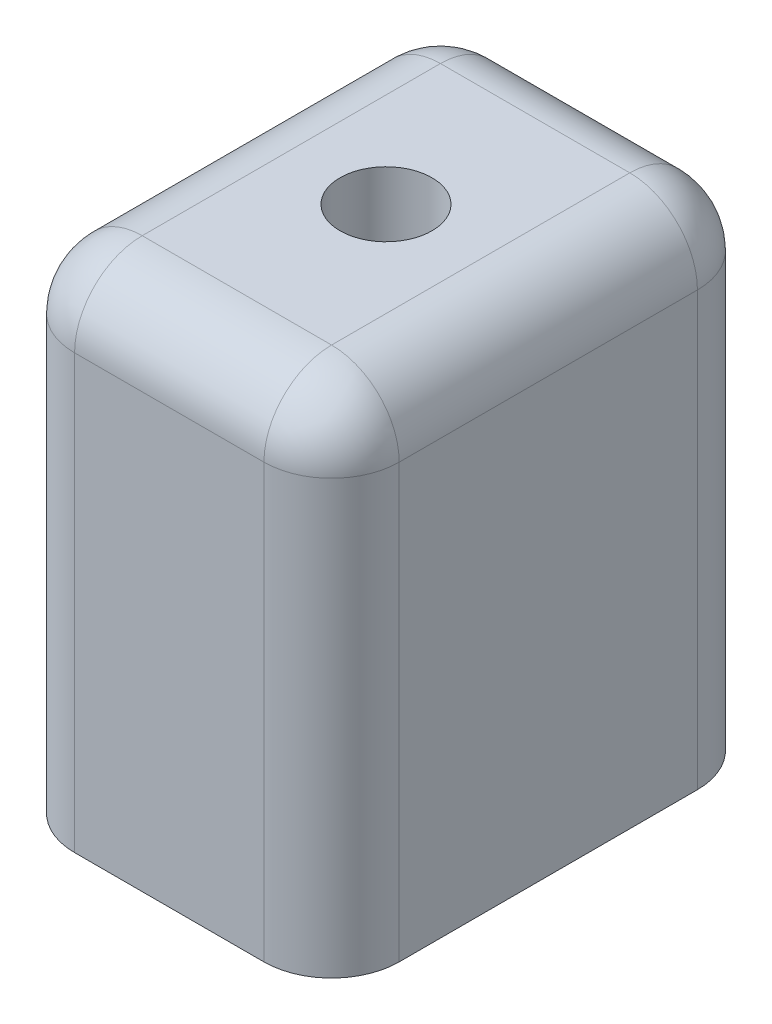
SolidWorks part; units mm, degrees
ref_plane "Front Plane" through (0, 0, 0) normal (0, 0, 1) x (1, 0, 0)
ref_plane "Top Plane" through (0, 0, 0) normal (0, 1, 0) x (1, 0, 0)
ref_plane "Right Plane" through (0, 0, 0) normal (1, 0, 0) x (0, 0, -1)
sketch "Sketch1" plane through (0, 0, 0) normal (0, 1, 0) x (1, 0, 0)
  line L5 (-1.9438, 25.0455) -> (22.0562, 25.0455)
  line L6 (-1.9438, 25.0455) -> (-1.9438, -7.0045)
  line L7 (-1.9438, -7.0045) -> (22.0562, -7.0045)
  line L8 (22.0562, 25.0455) -> (22.0562, -7.0045)
  circle A0 centre (5.0562, 9.0205) radius 2.15
  circle A1 centre (15.0562, 9.0205) radius 2.15
  circle A2 centre (10.0562, 19.8955) radius 2.15
  circle A3 centre (10.0562, -1.8545) radius 2.15
  point P13 (22.0562, 9.0205)
  dimension "D1" = 4.3
  dimension "D2" = 4.3
  dimension "D6" = 4.3
  dimension "D7" = 4.3
  dimension "D10" = 7
  dimension "D3" = 10
  dimension "D4" = 5
  dimension "D5" = 5
  dimension "D8" = 21.75
  dimension "D9" = 10.875
  dimension "D11" = 7
  dimension "D12" = 24
  dimension "D13" = 5.15
  dimension "D14" = 5.15
extrude "Boss-Extrude1" add sketch "Sketch1" along normal blind 37
sketch "Sketch2" plane through (0, 37, 0) normal (0, 1, 0) x (1, 0, 0)
  circle A0 centre (10.0562, 19.8955) radius 2.15
  circle A1 centre (15.0562, 9.0205) radius 2.15
  circle A2 centre (10.0562, -1.8545) radius 2.15
  circle A3 centre (5.0562, 9.0205) radius 2.15
extrude "Boss-Extrude2" add sketch "Sketch2" against normal blind 30
sketch "Sketch3" plane through (0, 37, 0) normal (0, 1, 0) x (1, 0, 0)
  line L0 (22.0562, -7.0045) -> (22.0562, 25.0455) construction
  line L1 (-1.9438, -7.0045) -> (22.0562, -7.0045) construction
  circle A0 centre (10.0562, 9.0205) radius 3.4
  dimension "D1" = 6.8
  dimension "D2" = 12
  dimension "D3" = 16.025
extrude "Cut-Extrude1" cut sketch "Sketch3" against normal blind 12
fillet "Fillet1" radius 5 8 edges at (10.0562, 37, -25.0455) (22.0562, 37, -9.0205) (10.0562, 37, 7.0045) (-1.9438, 37, -9.0205) (22.0562, 18.5, 7.0045) (-1.9438, 18.5, 7.0045) (-1.9438, 18.5, -25.0455) (22.0562, 18.5, -25.0455)
sketch "Sketch4" plane through (-1.9438, 0, 0) normal (-1, 0, 0) x (0, 0, 1)
  line L0 (7.0045, 32) -> (7.0045, 0) construction
  line L1 (-20.0455, 0) -> (2.0045, 0) construction
  circle A0 centre (-9.0205, 4) radius 2.75
  dimension "D2" = 5.5
  dimension "D1" = 16.025
  dimension "D3" = 4
extrude "Boss-Extrude3" add sketch "Sketch4" along normal blind 5
fillet "Fillet2" radius 1.5 1 edges at (-6.9438, 4, -6.2705)
